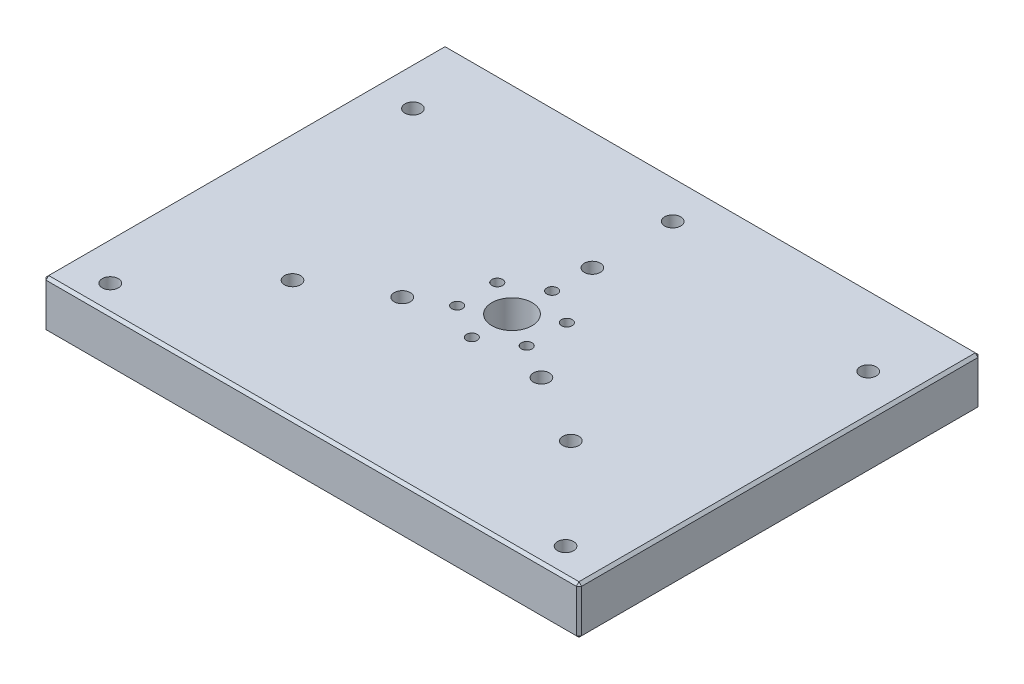
SolidWorks part; units mm, degrees
ref_plane "Front" through (0, 0, 0) normal (0, 0, 1) x (1, 0, 0)
ref_plane "Top" through (0, 0, 0) normal (0, 1, 0) x (1, 0, 0)
ref_plane "Right" through (0, 0, 0) normal (1, 0, 0) x (0, 0, -1)
sketch "Sketch1" plane through (0, 0, 0) normal (0, 1, 0) x (1, 0, 0)
  line L0 (0, -50) -> (0, 50) construction
  line L1 (-100, 75) -> (100, 75)
  line L2 (-100, 75) -> (-100, -75)
  line L3 (-100, -75) -> (100, -75)
  line L4 (100, 75) -> (100, -75)
  line L5 (-100, 75) -> (100, -75) construction
  line L6 (-100, -75) -> (100, 75) construction
  circle A0 centre (0, 0) radius 7.5
  circle A1 centre (0, 15) radius 2
  circle A2 centre (12.9904, 7.5) radius 2
  circle A3 centre (12.9904, -7.5) radius 2
  circle A4 centre (0, -15) radius 2
  circle A5 centre (-12.9904, -7.5) radius 2
  circle A6 centre (-12.9904, 7.5) radius 2
  point P0 (0, 0)
  point P24 (0, 0)
  dimension "D3" = 15
  dimension "D4" = 4
  dimension "D1" = 200
  dimension "D2" = 150
  dimension "D5" = 15
  dimension "D6" = 6
extrude "Boss-Extrude1" add sketch "Sketch1" along normal blind 8 and the other way blind 10
sketch "Sketch2" plane through (0, 0, 0) normal (0, 1, 0) x (1, 0, 0)
  line L0 (85, 65.6711) -> (85, -65.4482) construction
  line L1 (-50, 0) -> (50, 0) construction
  line L2 (0, 15) -> (0, 0) construction
  line L4 (0, 0) -> (12.9904, 7.5) construction
  line L5 (0, 0) -> (108.0478, -62.3815) construction
  line L6 (0, 0) -> (-130.0484, -75.0835) construction
  line L7 (100, -75) -> (100, 75) construction
  line L8 (-85, 65.6711) -> (-85, -65.4482) construction
  line L9 (-70, -56.3857) -> (-70, -46.4676) construction
  circle A0 centre (-25.9808, -15) radius 3
  circle A1 centre (0, 30) radius 3
  circle A2 centre (25.9808, -15) radius 3
  circle A3 centre (85, 48) radius 3
  circle A4 centre (85, -65) radius 3
  circle A5 centre (-51.9615, -30) radius 3
  circle A6 centre (-85, -65) radius 3
  circle A7 centre (-85, 48) radius 3
  circle A8 centre (0, 60) radius 3
  circle A9 centre (51.9615, -30) radius 3
  point P22 (0, 0)
  point P43 (0, 0)
  dimension "D3" = 6
  dimension "D5" = 3
  dimension "D6" = 15
  dimension "D7" = 6
  dimension "D9" = 6
  dimension "D10" = 65
  dimension "D11" = 6
  dimension "D1" = 60
  dimension "D2" = 120
  dimension "D4" = 30
  dimension "D8" = 48
  dimension "D12" = 15
  dimension "D13" = 30
  dimension "D14" = 3
extrude "Cut-Extrude2" cut sketch "Sketch2" against normal blind 10 and the other way blind 10
chamfer "Chamfer2" distance 1 angle 45 12 edges at (100, -1, -75) (100, -10, 0) (100, 8, 0) (100, -1, 75) (0, -10, 75) (0, 8, 75) (-100, -1, 75) (-100, 8, 0) (0, 8, -75) (-100, -1, -75) (0, -10, -75) (-100, -10, 0)
